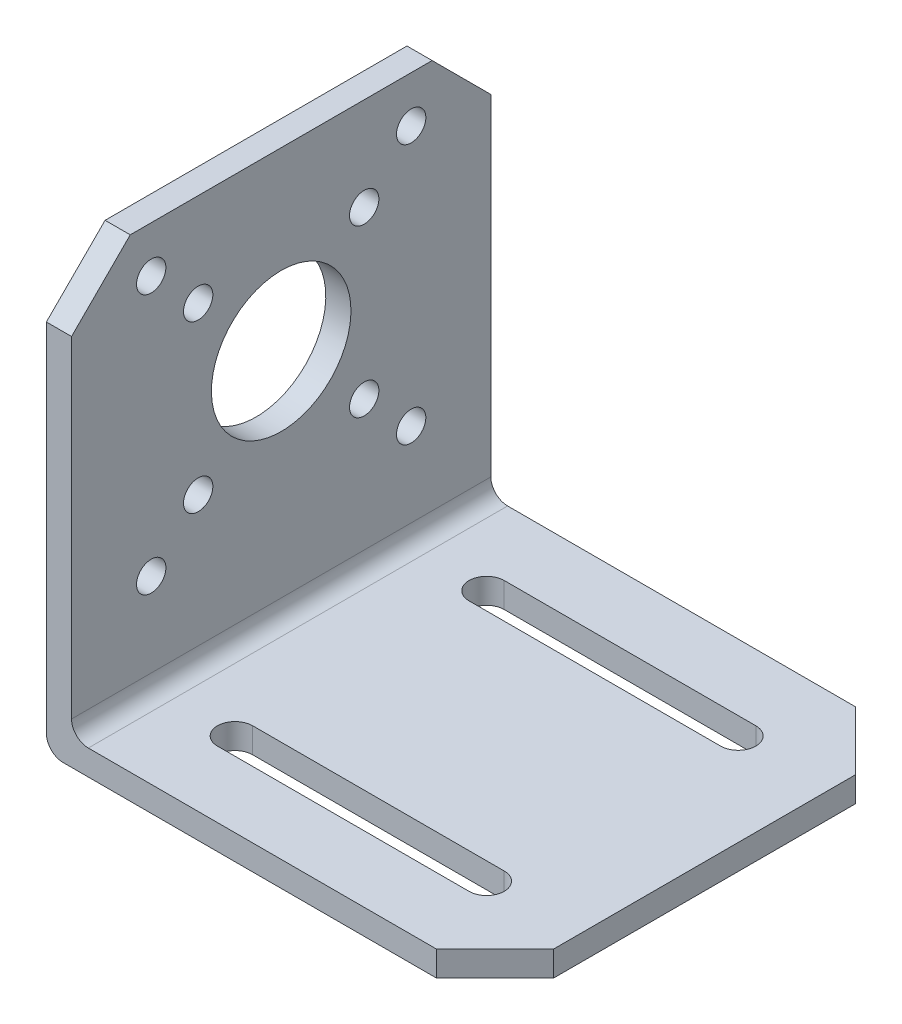
SolidWorks part; units mm, degrees
ref_plane "Front Plane" through (0, 0, 0) normal (0, 0, 1) x (1, 0, 0)
ref_plane "Top Plane" through (0, 0, 0) normal (0, 1, 0) x (1, 0, 0)
ref_plane "Right Plane" through (0, 0, 0) normal (1, 0, 0) x (0, 0, -1)
sketch "Sketch1" plane through (0, 0, 0) normal (0, 0, 1) x (1, 0, 0)
  line L0 (0, 51.5) -> (0, 2)
  line L1 (2, 0) -> (53.5, 0)
  line L2 (0, 51.5) -> (3, 51.5)
  line L3 (3, 51.5) -> (3, 5)
  line L4 (5, 3) -> (53.5, 3)
  line L5 (53.5, 3) -> (53.5, 0)
  arc A0 (5, 3) -> (3, 5) centre (5, 5) cw
  arc A1 (2, 0) -> (0, 2) centre (2, 2) cw
  point P3 (53.5, 1.5)
  point P12 (0, 0)
  dimension "D5" = 2
  dimension "D6" = 2
  dimension "D1" = 51.5
  dimension "D2" = 53.5
  dimension "D3" = 3
  dimension "D4" = 3
extrude "Boss-Extrude1" add sketch "Sketch1" along normal blind 50 contours L0 A1 L1 L5 L4 A0 L3 L2
sketch "Sketch2" plane through (3, 0, 0) normal (1, 0, 0) x (0, 0, -1)
  line L0 (-50, 51.5) -> (0, 51.5) construction
  line L1 (0, 51.5) -> (-50, 51.5) construction
  line L2 (-25, 51.5) -> (-25, 30.5) construction
  line L3 (-25, 30.5) -> (-52.5459, 30.5) construction
  line L4 (-25, 30.5) -> (-41.1849, 46.6849) construction
  circle A0 centre (-25, 30.5) radius 8.3201
  circle A1 centre (-25, 30.5) radius 14 construction
  circle A2 centre (-34.8995, 40.3995) radius 1.75
  circle A3 centre (-15.1005, 40.3995) radius 1.75
  circle A4 centre (-15.1005, 20.6005) radius 1.75
  circle A5 centre (-34.8995, 20.6005) radius 1.75
  circle A6 centre (-40.5, 46) radius 1.75
  circle A7 centre (-9.5, 46) radius 1.75
  circle A8 centre (-40.5, 15) radius 1.75
  circle A9 centre (-9.5, 15) radius 1.75
  point P8 (-25, 51.5)
  dimension "D3" = 28
  dimension "D4" = 3.5
  dimension "D6" = 3.5
  dimension "D1" = 21
  dimension "D2" = 45
  dimension "D5" = 50
  dimension "D7" = 31
extrude "Cut-Extrude1" cut sketch "Sketch2" against normal through all
chamfer "Chamfer1" distance 7 angle 45 1 edges at (1.5, 51.5, 0)
chamfer "Chamfer2" distance 7 angle 45 3 edges at (53.5, 1.5, 0) (53.5, 1.5, 50) (1.5, 51.5, 50)
sketch "Sketch5" plane through (0, 3, 0) normal (0, 1, 0) x (1, 0, 0)
  line L0 (12.5, -10) -> (42.5, -10) construction
  line L1 (12.5, -7.9) -> (42.5, -7.9)
  line L2 (12.5, -12.1) -> (42.5, -12.1)
  line L3 (53.5, -43) -> (53.5, -7) construction
  line L5 (-12.8436, -25) -> (80.3788, -25) construction
  line L6 (5, 0) -> (46.5, 0) construction
  line L7 (12.5, -40) -> (42.5, -40) construction
  line L8 (12.5, -42.1) -> (42.5, -42.1)
  line L9 (12.5, -37.9) -> (42.5, -37.9)
  arc A0 (12.5, -7.9) -> (12.5, -12.1) centre (12.5, -10) ccw
  arc A1 (42.5, -12.1) -> (42.5, -7.9) centre (42.5, -10) ccw
  arc A2 (12.5, -42.1) -> (12.5, -37.9) centre (12.5, -40) cw
  arc A3 (42.5, -37.9) -> (42.5, -42.1) centre (42.5, -40) cw
  point P2 (27.5, -10)
  point P15 (27.5, -40)
  dimension "D3" = 2.1
  dimension "D1" = 30
  dimension "D2" = 11
  dimension "D4" = 25
  dimension "D5" = 15
extrude "Cut-Extrude2" cut sketch "Sketch5" against normal blind 50
